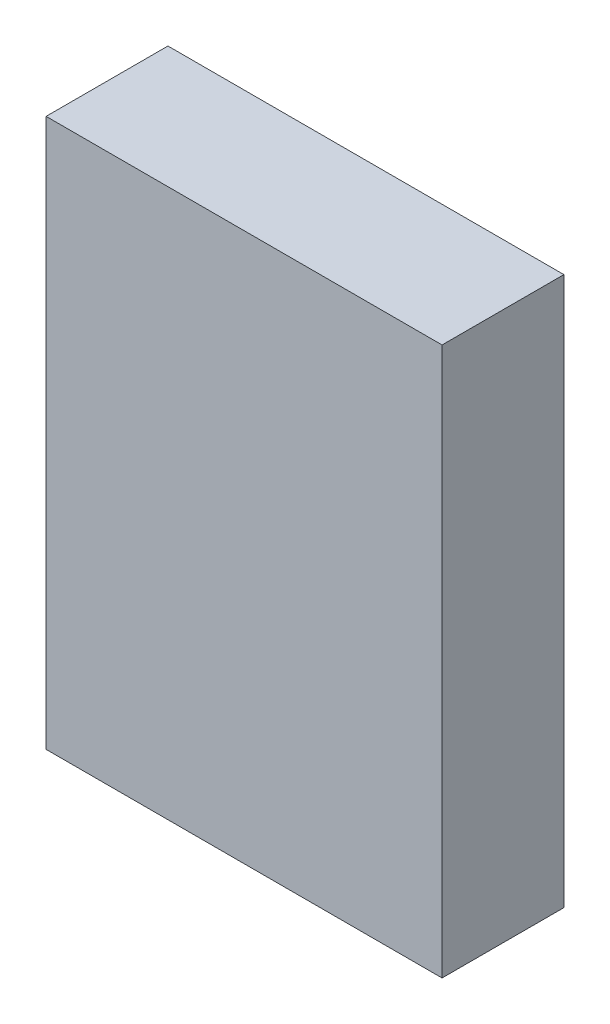
SolidWorks part; units mm, degrees
ref_plane "Plan de face" through (0, 0, 0) normal (0, 0, 1) x (1, 0, 0)
ref_plane "Plan de dessus" through (0, 0, 0) normal (0, 1, 0) x (1, 0, 0)
ref_plane "Plan de droite" through (0, 0, 0) normal (1, 0, 0) x (0, 0, -1)
sketch "Esquisse1" plane through (0, 0, 0) normal (0, 0, 1) x (1, 0, 0)
  line L1 (-5.6629, 10.8455) -> (13.8371, 10.8455)
  line L2 (-5.6629, 10.8455) -> (-5.6629, -16.1545)
  line L3 (-5.6629, -16.1545) -> (13.8371, -16.1545)
  line L4 (13.8371, 10.8455) -> (13.8371, -16.1545)
  dimension "D1" = 27
  dimension "D2" = 19.5
extrude "Boss.-Extru.1" add sketch "Esquisse1" along normal blind 6
